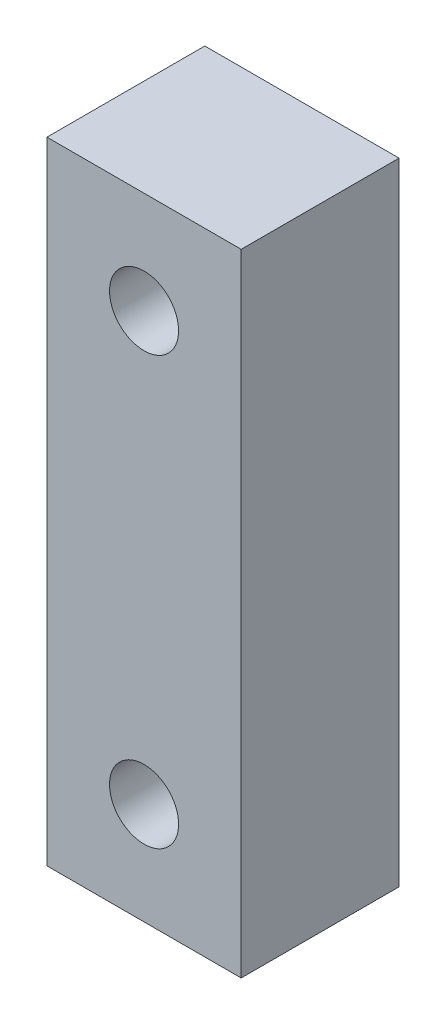
SolidWorks part; units mm, degrees
ref_plane "Plano frontal" through (0, 0, 0) normal (0, 0, 1) x (1, 0, 0)
ref_plane "Plano superior" through (0, 0, 0) normal (0, 1, 0) x (1, 0, 0)
ref_plane "Plano direito" through (0, 0, 0) normal (1, 0, 0) x (0, 0, -1)
ref_plane "Plano1" through (0, 0, 4.064) normal (0, 0, 1) x (1, 0, 0)
sketch "Esboço1" plane through (0, 0, 4.064) normal (0, 0, 1) x (1, 0, 0)
  line L0 (0, 16.245) -> (0, 0)
  line L1 (0, 0) -> (5, 0)
  line L2 (5, 0) -> (5, 16.245)
  line L3 (5, 16.245) -> (0, 16.245)
  circle A0 centre (2.5, 2.6225) radius 0.889
  circle A1 centre (2.5, 13.6225) radius 0.889
extrude "Ressalto-extrusão1" add sketch "Esboço1" against normal blind 4.064
